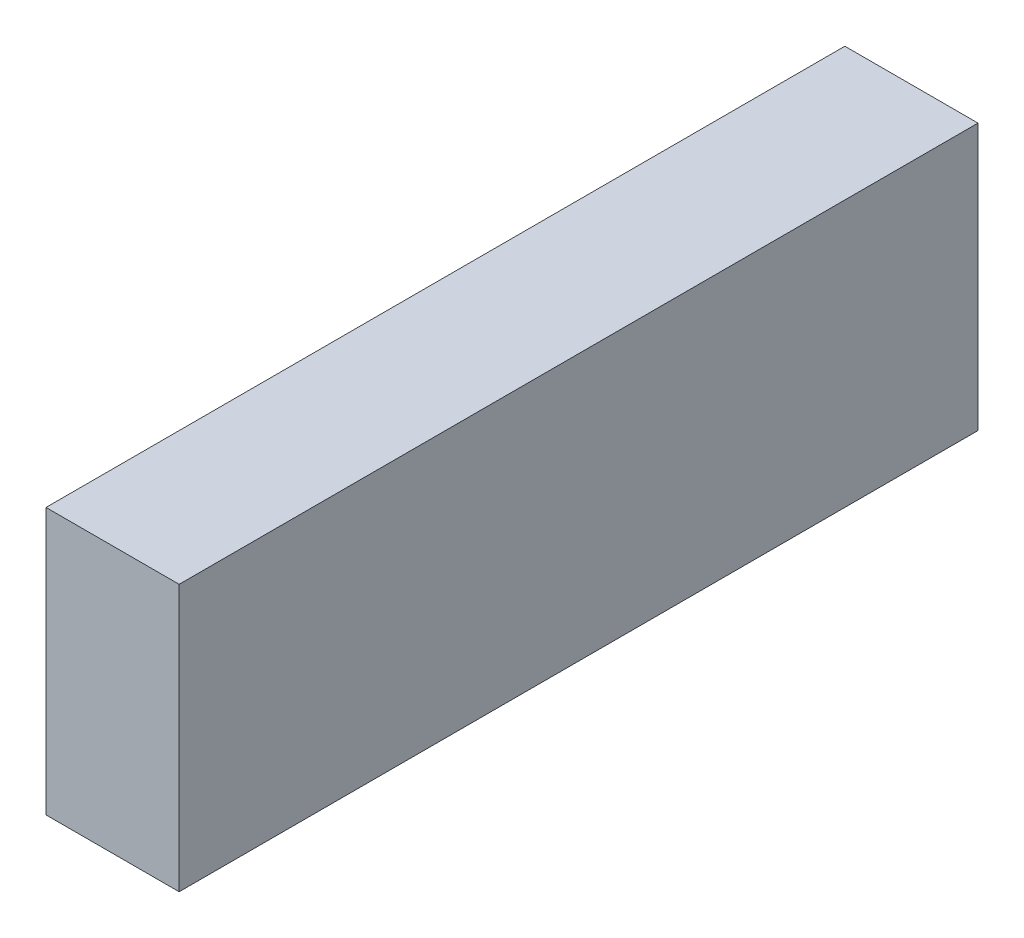
SolidWorks part; units mm, degrees
ref_plane "Front Plane" through (0, 0, 0) normal (0, 0, 1) x (1, 0, 0)
ref_plane "Top Plane" through (0, 0, 0) normal (0, 1, 0) x (1, 0, 0)
ref_plane "Right Plane" through (0, 0, 0) normal (1, 0, 0) x (0, 0, -1)
sketch "Sketch2" plane through (0, 0, 0) normal (1, 0, 0) x (0, 0, -1)
  line L3 (-262.7936, 0) -> (0, 0)
  line L4 (0, 0) -> (203.2, 0)
  line L6 (203.2, 0) -> (203.2, 81.9)
  line L7 (203.2, 81.9) -> (188.2, 81.9)
  line L8 (188.2, 81.9) -> (188.2, 20)
  line L9 (188.2, 20) -> (0, 20)
  line L10 (0, 20) -> (0, 133.7)
  line L11 (0, 133.7) -> (-115, 133.7)
  line L12 (-115, 133.7) -> (-171.1938, 94.3527)
  line L13 (-171.1938, 94.3527) -> (-262.7936, 81.4791)
  line L18 (-262.7936, 81.4791) -> (-262.7936, 31.4791)
  line L19 (-262.7936, 31.4791) -> (-262.7936, 0) construction
  arc A2 (-262.7936, 31.4791) -> (-262.7936, 0) centre (-255.1441, 15.7396) ccw
  dimension "D12" = 17.5
  dimension "D2" = 113.7
  dimension "D3" = 20
  dimension "D4" = 35
  dimension "D5" = 153
  dimension "D6" = 203.2
  dimension "D7" = 15
  dimension "D8" = 61.9
  dimension "D9" = 92.5
  dimension "D10" = 68.6
  dimension "D11" = 50
  dimension "D13" = 115
extrude "Boss-Extrude1" add sketch "Sketch2" along normal mid plane 138
sketch "Sketch4" plane through (0, 20, 0) normal (0, 1, 0) x (1, 0, 0)
  line L0 (69, 188.2) -> (-69, 188.2) construction
  line L1 (69, 0) -> (54, 0)
  line L2 (69, 0) -> (69, 188.2)
  line L3 (69, 188.2) -> (54, 188.2)
  line L4 (54, 0) -> (54, 188.2)
  dimension "D1" = 15
extrude "Boss-Extrude2" add sketch "Sketch4" along normal up to surface (61.9 mm away) up to face at (0, 81.9, -195.7)
mirror "Mirror1" about plane through (0, 0, 0) normal (1, 0, 0) of "Boss-Extrude2"
sketch "Sketch5" plane through (69, 0, 0) normal (1, 0, 0) x (0, 0, -1)
  line L0 (-262.7936, 0) -> (203.2, 0) construction
  line L1 (-224.9441, 0) -> (-160.3441, 0)
  line L2 (42.0559, 0) -> (106.6559, 0)
  arc A0 (-224.9441, 0) -> (-160.3441, 0) centre (-192.6441, 0) ccw
  arc A1 (42.0559, 0) -> (106.6559, 0) centre (74.3559, 0) ccw
  arc A2 (-262.7936, 31.4791) -> (-262.7936, 0) centre (-255.1441, 15.7396) ccw construction
  point P11 (-272.6441, 15.7396)
  dimension "D3" = 32.3
  dimension "D1" = 347
  dimension "D2" = 80
extrude "Boss-Extrude3" add sketch "Sketch5" against normal blind 20.4
mirror "Mirror2" about plane through (0, 0, 0) normal (1, 0, 0) of "Boss-Extrude3"
fillet "Fillet1" radius 10 5 edges at (0, 133.7, 0) (0, 133.7, 115) (0, 94.3527, 171.1938) (0, 81.4791, 262.7936) (0, 31.4791, 262.7936)
sketch "Sketch6" plane through (0, 0, 0) normal (1, 0, 0) x (0, 0, -1)
  line L0 (-192.6441, 0) -> (-192.6441, -32.3) construction
  line L1 (-2192.6441, -32.3) -> (3807.3559, -32.3)
  line L2 (-2192.6441, -32.3) -> (-2192.6441, 1967.7)
  line L3 (-2192.6441, 1967.7) -> (3807.3559, 1967.7)
  line L4 (3807.3559, -32.3) -> (3807.3559, 1967.7)
  arc A0 (-224.9441, 0) -> (-160.3441, 0) centre (-192.6441, 0) ccw construction
  dimension "D1" = 2000
  dimension "D2" = 6000
  dimension "D3" = 2000
extrude "Boss-Extrude4" add sketch "Sketch6" along normal blind 1000 separate body
sketch "Sketch8" plane through (0, 0, 0) normal (1, 0, 0) x (0, 0, -1)
  line L1 (-392.6441, -32.3) -> (487.3559, -32.3)
  line L2 (-392.6441, -32.3) -> (-392.6441, 407.7)
  line L3 (-392.6441, 407.7) -> (487.3559, 407.7)
  line L4 (487.3559, -32.3) -> (487.3559, 407.7)
  arc A0 (-224.9441, 0) -> (-160.3441, 0) centre (-192.6441, 0) ccw construction
  point P7 (-192.6441, -32.3)
  dimension "D1" = 880
  dimension "D2" = 440
  dimension "D3" = 200
extrude "Boss-Extrude5" add sketch "Sketch8" along normal blind 220 separate body
sketch "Sketch9" plane through (0, 20, 0) normal (0, 1, 0) x (1, 0, 0)
  line L1 (54, 0) -> (-54, 0)
  line L2 (54, 0) -> (54, 188.2)
  line L3 (54, 188.2) -> (-54, 188.2)
  line L4 (-54, 0) -> (-54, 188.2)
extrude "Boss-Extrude6" add sketch "Sketch9" along normal up to surface (61.9 mm away) up to face at (0, 81.9, -97.85)
sketch "Sketch10" plane through (69, 0, 0) normal (1, 0, 0) x (0, 0, -1)
  line L0 (203.2, 81.9) -> (193.2, 81.9)
  line L1 (203.2, 81.9) -> (0, 81.9) construction
  line L2 (193.2, 81.9) -> (203.2, 98.9)
  line L3 (203.2, 98.9) -> (203.2, 81.9)
  dimension "D1" = 17
  dimension "D2" = 10
extrude "Boss-Extrude7" add sketch "Sketch10" against normal up to surface (138 mm away) up to face at (-69, 57.5498, 96.0134)
